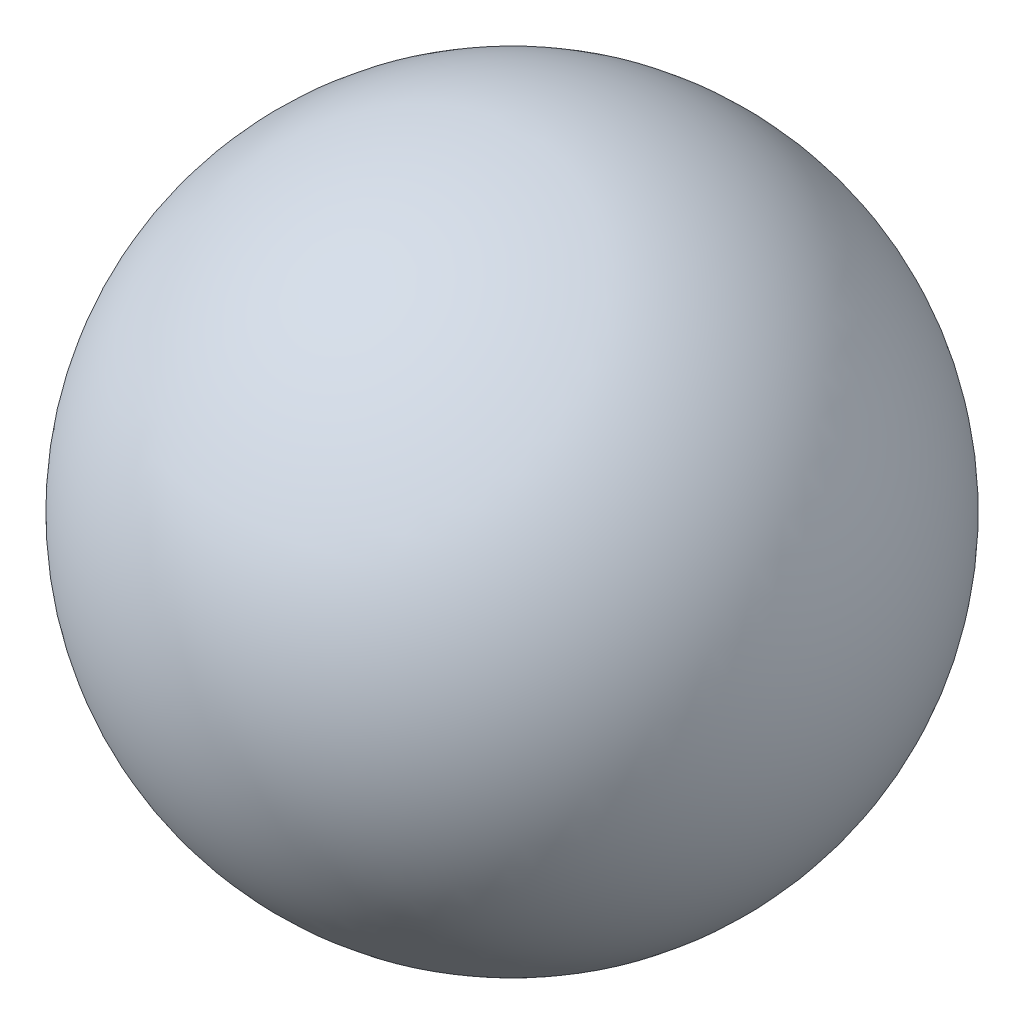
SolidWorks part; units mm, degrees
ref_plane "Front Plane" through (0, 0, 0) normal (0, 0, 1) x (1, 0, 0)
ref_plane "Top Plane" through (0, 0, 0) normal (0, 1, 0) x (1, 0, 0)
ref_plane "Right Plane" through (0, 0, 0) normal (1, 0, 0) x (0, 0, -1)
sketch "Sketch1" plane through (0, 0, 0) normal (0, 0, 1) x (1, 0, 0)
  line L0 (0, 125) -> (0, 105)
  line L1 (0, -105) -> (0, -125)
  line L2 (0, 105) -> (0, -105) construction
  arc A0 (0, -125) -> (0, 125) centre (0, 0) ccw
  arc A1 (0, -105) -> (0, 105) centre (0, 0) ccw
  dimension "D1" = 250
  dimension "D2" = 210
revolve "Revolve1" add sketch "Sketch1" angle 360 about L2
